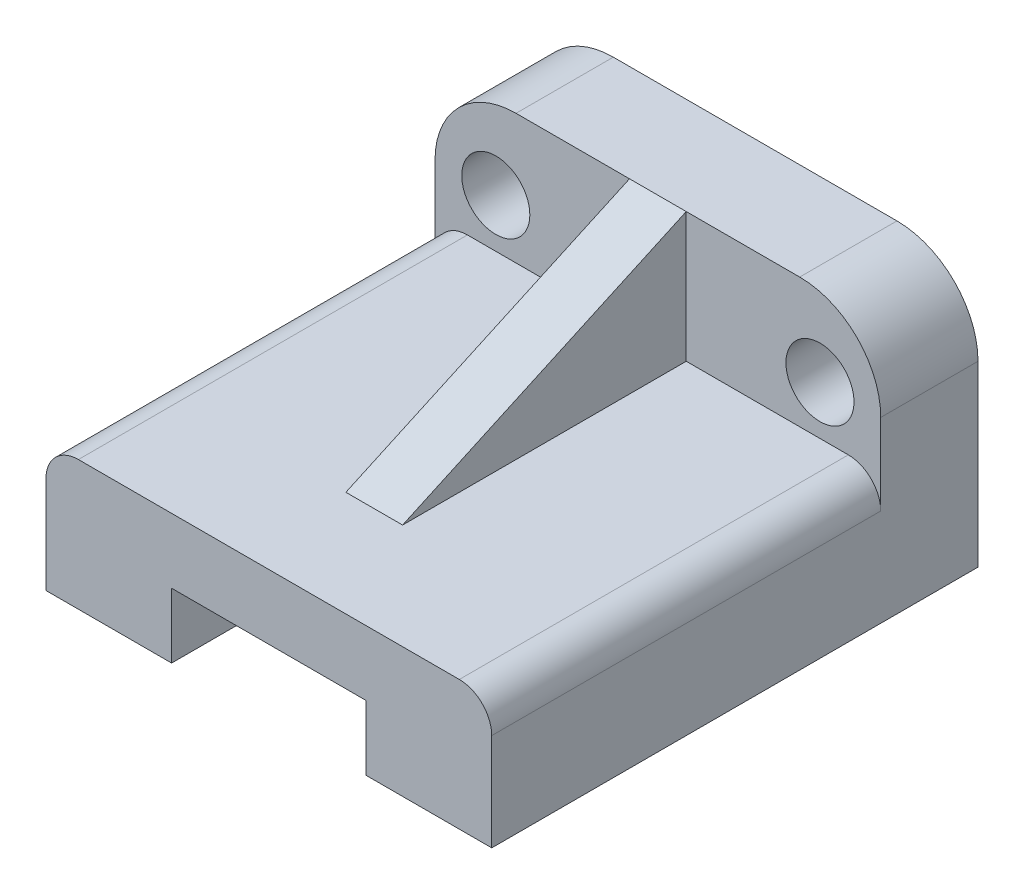
SolidWorks part; units mm, degrees
ref_plane "Ön Düzlem" through (0, 0, 0) normal (0, 0, 1) x (1, 0, 0)
ref_plane "Üst Düzlem" through (0, 0, 0) normal (0, 1, 0) x (1, 0, 0)
ref_plane "Sağ Düzlem" through (0, 0, 0) normal (1, 0, 0) x (0, 0, -1)
sketch "Çizim1" plane through (0, 0, 0) normal (0, 0, 1) x (1, 0, 0)
  line L0 (0, 0) -> (0, 40.4111) construction
  line L1 (-17.5, 16) -> (17.5, 16)
  line L2 (-27.5, 6) -> (-27.5, -16)
  line L3 (-27.5, -16) -> (27.5, -16)
  line L4 (27.5, 6) -> (27.5, -16)
  line L5 (-27.5, 16) -> (27.5, -16) construction
  line L6 (-27.5, -16) -> (27.5, 16) construction
  arc A0 (-17.5, 16) -> (-27.5, 6) centre (-17.5, 6) ccw
  arc A1 (17.5, 16) -> (27.5, 6) centre (17.5, 6) cw
  circle A4 centre (-20, 6) radius 4.2
  circle A5 centre (20, 6) radius 4.2
  point P0 (0, 0)
  dimension "D3" = 10
  dimension "D4" = 8.4
  dimension "D1" = 32
  dimension "D2" = 55
  dimension "D5" = 20
  dimension "D6" = 10
extrude "Yükseklik-Ekstrüzyon1" add sketch "Çizim1" along normal blind 12
sketch "Çizim2" plane through (0, 0, 12) normal (0, 0, 1) x (1, 0, 0)
  line L0 (27.5, -16) -> (27.5, 6) construction
  line L1 (-27.5, -16) -> (-12, -16)
  line L2 (-27.5, -16) -> (-27.5, -4)
  line L3 (-23.5, 0) -> (23.5, 0)
  line L4 (27.5, -16) -> (27.5, -4)
  line L5 (12, -16) -> (27.5, -16)
  line L7 (-12, -16) -> (-12, -8)
  line L8 (-12, -8) -> (12, -8)
  line L9 (12, -16) -> (12, -8)
  arc A0 (23.5, 0) -> (27.5, -4) centre (23.5, -4) cw
  arc A1 (-27.5, -4) -> (-23.5, 0) centre (-23.5, -4) cw
  point P9 (27.5, 0)
  point P12 (-27.5, 0)
  point P19 (11.0024, -8)
  point P20 (0, -8)
  dimension "D2" = 4
  dimension "D1" = 16
  dimension "D3" = 8
  dimension "D4" = 24
extrude "Yükseklik-Ekstrüzyon2" add sketch "Çizim2" along normal blind 48
sketch "Çizim3" plane through (0, 0, 0) normal (1, 0, 0) x (0, 0, -1)
  line L0 (-12, 16) -> (-47, 0)
  line L1 (-60, 0) -> (-12, 0) construction
  line L2 (-47, 0) -> (-12, 0)
  line L3 (-12, 0) -> (-12, 16)
  dimension "D1" = 35
extrude "Yükseklik-Ekstrüzyon3" add sketch "Çizim3" along normal mid plane 7
